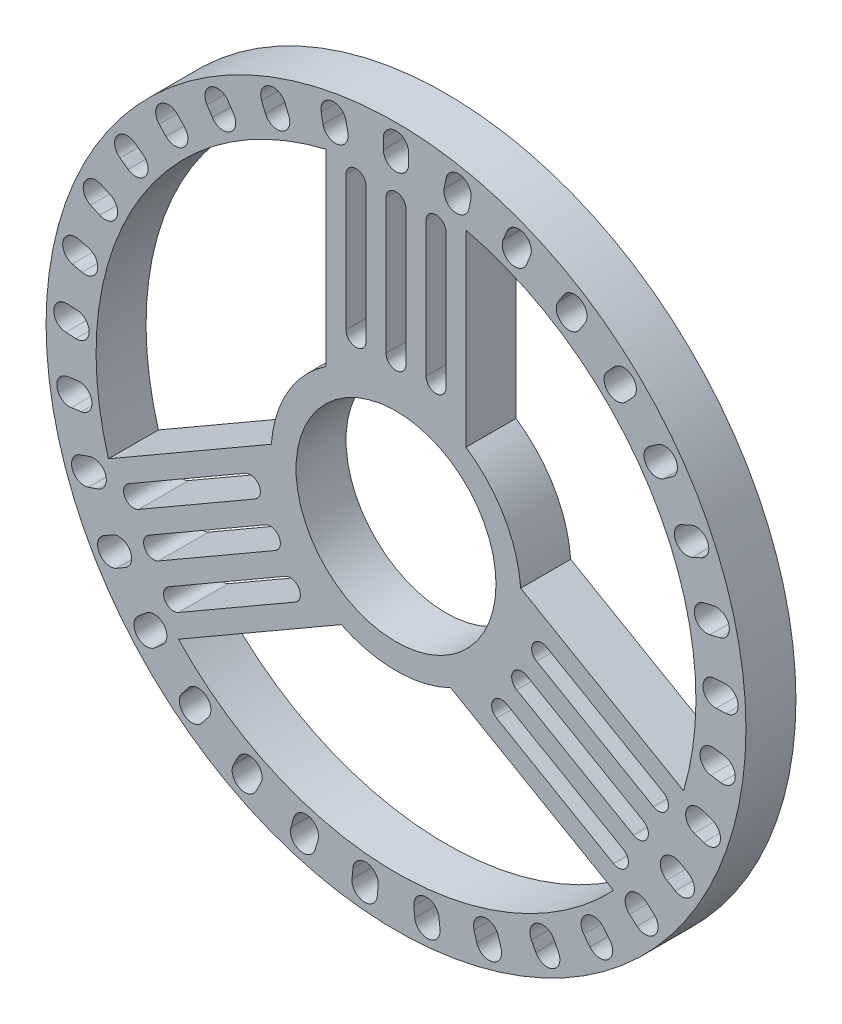
SolidWorks part; units mm, degrees
ref_plane "前视基准面" through (0, 0, 0) normal (0, 0, 1) x (1, 0, 0)
ref_plane "上视基准面" through (0, 0, 0) normal (0, 1, 0) x (1, 0, 0)
ref_plane "右视基准面" through (0, 0, 0) normal (1, 0, 0) x (0, 0, -1)
sketch "草图1" plane through (0, 0, 0) normal (0, 0, 1) x (1, 0, 0)
  line L0 (2.7274, -5.6161) -> (10.8818, -10.3241)
  line L1 (6.2305, 0.4443) -> (14.3818, -4.2619)
  line L2 (0, 16.5) -> (0, 16) construction
  line L3 (0.6338, 16.5) -> (0.6338, 16)
  line L4 (-0.6338, 16.5) -> (-0.6338, 16)
  line L5 (3.1226, 16.2018) -> (3.028, 15.7109) construction
  line L6 (3.745, 16.0819) -> (3.6504, 15.5909)
  line L7 (2.5003, 16.3218) -> (2.4057, 15.8308)
  line L8 (6.1324, 15.3181) -> (5.9466, 14.8539) construction
  line L9 (6.7208, 15.0825) -> (6.535, 14.6183)
  line L10 (5.544, 15.5536) -> (5.3582, 15.0894)
  line L11 (8.9206, 13.8807) -> (8.6503, 13.4601) construction
  line L12 (9.4538, 13.538) -> (9.1834, 13.1174)
  line L13 (8.3874, 14.2233) -> (8.1171, 13.8027)
  line L14 (11.3863, 11.9416) -> (11.0413, 11.5797) construction
  line L15 (11.845, 11.5042) -> (11.5, 11.1424)
  line L16 (10.9276, 12.379) -> (10.5826, 12.0171)
  line L17 (13.4405, 9.5709) -> (13.0332, 9.2809) construction
  line L18 (13.8081, 9.0547) -> (13.4009, 8.7646)
  line L19 (13.0729, 10.0872) -> (12.6656, 9.7972)
  line L20 (15.0089, 6.8543) -> (14.5541, 6.6466) construction
  line L21 (15.2722, 6.2778) -> (14.8174, 6.0701)
  line L22 (14.7456, 7.4309) -> (14.2908, 7.2232)
  line L23 (16.0349, 3.89) -> (15.549, 3.7721) construction
  line L24 (16.1843, 3.2741) -> (15.6984, 3.1562)
  line L25 (15.8855, 4.506) -> (15.3996, 4.3881)
  line L26 (16.4813, 0.7851) -> (15.9819, 0.7613) construction
  line L27 (16.5115, 0.152) -> (16.012, 0.1282)
  line L28 (16.4512, 1.4182) -> (15.9517, 1.3944)
  line L29 (16.3321, -2.3482) -> (15.8371, -2.277) construction
  line L30 (16.2419, -2.9755) -> (15.7469, -2.9044)
  line L31 (16.4223, -1.7208) -> (15.9273, -1.6497)
  line L32 (15.5925, -5.3966) -> (15.12, -5.2331) construction
  line L33 (15.3852, -5.9956) -> (14.9127, -5.832)
  line L34 (15.7998, -4.7977) -> (15.3273, -4.6341)
  line L35 (14.2894, -8.25) -> (13.8564, -8) construction
  line L36 (13.9725, -8.7989) -> (13.5395, -8.5489)
  line L37 (14.6063, -7.7011) -> (14.1733, -7.4511)
  line L38 (12.4699, -10.8052) -> (12.092, -10.4778) construction
  line L39 (12.0548, -11.2842) -> (11.6769, -10.9568)
  line L40 (12.8849, -10.3262) -> (12.507, -9.9988)
  line L41 (10.1996, -12.9699) -> (9.8905, -12.5768) construction
  line L42 (9.7014, -13.3617) -> (9.3923, -12.9686)
  line L43 (10.6978, -12.5781) -> (10.3887, -12.1851)
  line L44 (7.5607, -14.6658) -> (7.3316, -14.2214) construction
  line L45 (6.9974, -14.9562) -> (6.7683, -14.5118)
  line L46 (8.1241, -14.3754) -> (7.895, -13.9309)
  line L47 (4.6486, -15.8316) -> (4.5077, -15.3519) construction
  line L48 (4.0405, -16.0102) -> (3.8996, -15.5305)
  line L49 (5.2567, -15.6531) -> (5.1159, -15.1733)
  line L50 (1.5684, -16.4253) -> (1.5209, -15.9276) construction
  line L51 (0.9375, -16.4855) -> (0.89, -15.9878)
  line L52 (2.1994, -16.365) -> (2.1518, -15.8673)
  line L53 (-1.5684, -16.4253) -> (-1.5209, -15.9276) construction
  line L54 (-2.1994, -16.365) -> (-2.1518, -15.8673)
  line L55 (-0.9375, -16.4855) -> (-0.89, -15.9878)
  line L56 (-4.6486, -15.8316) -> (-4.5077, -15.3519) construction
  line L57 (-5.2567, -15.6531) -> (-5.1159, -15.1733)
  line L58 (-4.0405, -16.0102) -> (-3.8996, -15.5305)
  line L59 (-7.5607, -14.6658) -> (-7.3316, -14.2214) construction
  line L60 (-8.1241, -14.3754) -> (-7.895, -13.9309)
  line L61 (-6.9974, -14.9562) -> (-6.7683, -14.5118)
  line L62 (-10.1996, -12.9699) -> (-9.8905, -12.5768) construction
  line L63 (-10.6978, -12.5781) -> (-10.3887, -12.1851)
  line L64 (-9.7014, -13.3617) -> (-9.3923, -12.9686)
  line L65 (-12.4699, -10.8052) -> (-12.092, -10.4778) construction
  line L66 (-12.8849, -10.3262) -> (-12.507, -9.9988)
  line L67 (-12.0548, -11.2842) -> (-11.6769, -10.9568)
  line L68 (-14.2894, -8.25) -> (-13.8564, -8) construction
  line L69 (-14.6063, -7.7011) -> (-14.1733, -7.4511)
  line L70 (-13.9725, -8.7989) -> (-13.5395, -8.5489)
  line L71 (-15.5925, -5.3966) -> (-15.12, -5.2331) construction
  line L72 (-15.7998, -4.7977) -> (-15.3273, -4.6341)
  line L73 (-15.3852, -5.9956) -> (-14.9127, -5.832)
  line L74 (-16.3321, -2.3482) -> (-15.8371, -2.277) construction
  line L75 (-16.4223, -1.7208) -> (-15.9273, -1.6497)
  line L76 (-16.2419, -2.9755) -> (-15.7469, -2.9044)
  line L77 (-16.4813, 0.7851) -> (-15.9819, 0.7613) construction
  line L78 (-16.4512, 1.4182) -> (-15.9517, 1.3944)
  line L79 (-16.5115, 0.152) -> (-16.012, 0.1282)
  line L80 (-16.0349, 3.89) -> (-15.549, 3.7721) construction
  line L81 (-15.8855, 4.506) -> (-15.3996, 4.3881)
  line L82 (-16.1843, 3.2741) -> (-15.6984, 3.1562)
  line L83 (-15.0089, 6.8543) -> (-14.5541, 6.6466) construction
  line L84 (-14.7456, 7.4309) -> (-14.2908, 7.2232)
  line L85 (-15.2722, 6.2778) -> (-14.8174, 6.0701)
  line L86 (-13.4405, 9.5709) -> (-13.0332, 9.2809) construction
  line L87 (-13.0729, 10.0872) -> (-12.6656, 9.7972)
  line L88 (-13.8081, 9.0547) -> (-13.4009, 8.7646)
  line L89 (-11.3863, 11.9416) -> (-11.0413, 11.5797) construction
  line L90 (-10.9276, 12.379) -> (-10.5826, 12.0171)
  line L91 (-11.845, 11.5042) -> (-11.5, 11.1424)
  line L92 (-8.9206, 13.8807) -> (-8.6503, 13.4601) construction
  line L93 (-8.3874, 14.2233) -> (-8.1171, 13.8027)
  line L94 (-9.4538, 13.538) -> (-9.1834, 13.1174)
  line L95 (-6.1324, 15.3181) -> (-5.9466, 14.8539) construction
  line L96 (-5.544, 15.5536) -> (-5.3582, 15.0894)
  line L97 (-6.7208, 15.0825) -> (-6.535, 14.6183)
  line L98 (-3.1226, 16.2018) -> (-3.028, 15.7109) construction
  line L99 (-2.5003, 16.3218) -> (-2.4057, 15.8308)
  line L100 (-3.745, 16.0819) -> (-3.6504, 15.5909)
  line L101 (12.1234, -6.9994) -> (6.283, -3.6275) construction
  line L102 (3.5, 5.1701) -> (3.5, 14.586)
  line L103 (-3.5, 5.1736) -> (-3.5, 14.586)
  line L104 (11.8737, -7.4319) -> (6.0333, -4.0599)
  line L105 (12.3731, -6.567) -> (6.5326, -3.195)
  line L106 (11.1234, -8.7315) -> (5.283, -5.3595) construction
  line L107 (0, 13.9989) -> (0, 7.2549) construction
  line L108 (0.4994, 13.9989) -> (0.4994, 7.2549)
  line L109 (-0.4994, 13.9989) -> (-0.4994, 7.2549)
  line L110 (2, 13.9989) -> (2, 7.2549) construction
  line L111 (2.4994, 13.9989) -> (2.4994, 7.2549)
  line L112 (1.5006, 13.9989) -> (1.5006, 7.2549)
  line L113 (-2, 13.9989) -> (-2, 7.2549) construction
  line L114 (-1.5006, 13.9989) -> (-1.5006, 7.2549)
  line L115 (-2.4994, 13.9989) -> (-2.4994, 7.2549)
  line L116 (10.8737, -9.164) -> (5.0333, -5.792)
  line L117 (11.3731, -8.299) -> (5.5326, -4.9271)
  line L118 (13.1234, -5.2674) -> (7.283, -1.8954) construction
  line L119 (12.8737, -5.6998) -> (7.0333, -2.3279)
  line L120 (13.3731, -4.8349) -> (7.5326, -1.463)
  line L121 (-6.2274, 0.4461) -> (-14.3818, -4.2619)
  line L122 (-2.7305, -5.6179) -> (-10.8818, -10.3241)
  line L123 (-12.1234, -6.9994) -> (-6.283, -3.6275) construction
  line L124 (-12.3731, -6.567) -> (-6.5326, -3.195)
  line L125 (-11.8737, -7.4319) -> (-6.0333, -4.0599)
  line L126 (-13.1234, -5.2674) -> (-7.283, -1.8954) construction
  line L127 (-13.3731, -4.8349) -> (-7.5326, -1.463)
  line L128 (-12.8737, -5.6998) -> (-7.0333, -2.3279)
  line L129 (-11.1234, -8.7315) -> (-5.283, -5.3595) construction
  line L130 (-11.3731, -8.299) -> (-5.5326, -4.9271)
  line L131 (-10.8737, -9.164) -> (-5.0333, -5.792)
  circle A0 centre (0, 0) radius 17.5
  circle A1 centre (0, 0) radius 15
  circle A2 centre (0, 0) radius 5
  circle A3 centre (0, 0) radius 6.25
  arc A4 (0.6338, 16.5) -> (-0.6338, 16.5) centre (0, 16.5) ccw
  arc A5 (-0.6338, 16) -> (0.6338, 16) centre (0, 16) ccw
  arc A6 (3.745, 16.0819) -> (2.5003, 16.3218) centre (3.1226, 16.2018) ccw
  arc A7 (2.4057, 15.8308) -> (3.6504, 15.5909) centre (3.028, 15.7109) ccw
  arc A8 (6.7208, 15.0825) -> (5.544, 15.5536) centre (6.1324, 15.3181) ccw
  arc A9 (5.3582, 15.0894) -> (6.535, 14.6183) centre (5.9466, 14.8539) ccw
  arc A10 (9.4538, 13.538) -> (8.3874, 14.2233) centre (8.9206, 13.8807) ccw
  arc A11 (8.1171, 13.8027) -> (9.1834, 13.1174) centre (8.6503, 13.4601) ccw
  arc A12 (11.845, 11.5042) -> (10.9276, 12.379) centre (11.3863, 11.9416) ccw
  arc A13 (10.5826, 12.0171) -> (11.5, 11.1424) centre (11.0413, 11.5797) ccw
  arc A14 (13.8081, 9.0547) -> (13.0729, 10.0872) centre (13.4405, 9.5709) ccw
  arc A15 (12.6656, 9.7972) -> (13.4009, 8.7646) centre (13.0332, 9.2809) ccw
  arc A16 (15.2722, 6.2778) -> (14.7456, 7.4309) centre (15.0089, 6.8543) ccw
  arc A17 (14.2908, 7.2232) -> (14.8174, 6.0701) centre (14.5541, 6.6466) ccw
  arc A18 (16.1843, 3.2741) -> (15.8855, 4.506) centre (16.0349, 3.89) ccw
  arc A19 (15.3996, 4.3881) -> (15.6984, 3.1562) centre (15.549, 3.7721) ccw
  arc A20 (16.5115, 0.152) -> (16.4512, 1.4182) centre (16.4813, 0.7851) ccw
  arc A21 (15.9517, 1.3944) -> (16.012, 0.1282) centre (15.9819, 0.7613) ccw
  arc A22 (16.2419, -2.9755) -> (16.4223, -1.7208) centre (16.3321, -2.3482) ccw
  arc A23 (15.9273, -1.6497) -> (15.7469, -2.9044) centre (15.8371, -2.277) ccw
  arc A24 (15.3852, -5.9956) -> (15.7998, -4.7977) centre (15.5925, -5.3966) ccw
  arc A25 (15.3273, -4.6341) -> (14.9127, -5.832) centre (15.12, -5.2331) ccw
  arc A26 (13.9725, -8.7989) -> (14.6063, -7.7011) centre (14.2894, -8.25) ccw
  arc A27 (14.1733, -7.4511) -> (13.5395, -8.5489) centre (13.8564, -8) ccw
  arc A28 (12.0548, -11.2842) -> (12.8849, -10.3262) centre (12.4699, -10.8052) ccw
  arc A29 (12.507, -9.9988) -> (11.6769, -10.9568) centre (12.092, -10.4778) ccw
  arc A30 (9.7014, -13.3617) -> (10.6978, -12.5781) centre (10.1996, -12.9699) ccw
  arc A31 (10.3887, -12.1851) -> (9.3923, -12.9686) centre (9.8905, -12.5768) ccw
  arc A32 (6.9974, -14.9562) -> (8.1241, -14.3754) centre (7.5607, -14.6658) ccw
  arc A33 (7.895, -13.9309) -> (6.7683, -14.5118) centre (7.3316, -14.2214) ccw
  arc A34 (4.0405, -16.0102) -> (5.2567, -15.6531) centre (4.6486, -15.8316) ccw
  arc A35 (5.1159, -15.1733) -> (3.8996, -15.5305) centre (4.5077, -15.3519) ccw
  arc A36 (0.9375, -16.4855) -> (2.1994, -16.365) centre (1.5684, -16.4253) ccw
  arc A37 (2.1518, -15.8673) -> (0.89, -15.9878) centre (1.5209, -15.9276) ccw
  arc A38 (-2.1994, -16.365) -> (-0.9375, -16.4855) centre (-1.5684, -16.4253) ccw
  arc A39 (-0.89, -15.9878) -> (-2.1518, -15.8673) centre (-1.5209, -15.9276) ccw
  arc A40 (-5.2567, -15.6531) -> (-4.0405, -16.0102) centre (-4.6486, -15.8316) ccw
  arc A41 (-3.8996, -15.5305) -> (-5.1159, -15.1733) centre (-4.5077, -15.3519) ccw
  arc A42 (-8.1241, -14.3754) -> (-6.9974, -14.9562) centre (-7.5607, -14.6658) ccw
  arc A43 (-6.7683, -14.5118) -> (-7.895, -13.9309) centre (-7.3316, -14.2214) ccw
  arc A44 (-10.6978, -12.5781) -> (-9.7014, -13.3617) centre (-10.1996, -12.9699) ccw
  arc A45 (-9.3923, -12.9686) -> (-10.3887, -12.1851) centre (-9.8905, -12.5768) ccw
  arc A46 (-12.8849, -10.3262) -> (-12.0548, -11.2842) centre (-12.4699, -10.8052) ccw
  arc A47 (-11.6769, -10.9568) -> (-12.507, -9.9988) centre (-12.092, -10.4778) ccw
  arc A48 (-14.6063, -7.7011) -> (-13.9725, -8.7989) centre (-14.2894, -8.25) ccw
  arc A49 (-13.5395, -8.5489) -> (-14.1733, -7.4511) centre (-13.8564, -8) ccw
  arc A50 (-15.7998, -4.7977) -> (-15.3852, -5.9956) centre (-15.5925, -5.3966) ccw
  arc A51 (-14.9127, -5.832) -> (-15.3273, -4.6341) centre (-15.12, -5.2331) ccw
  arc A52 (-16.4223, -1.7208) -> (-16.2419, -2.9755) centre (-16.3321, -2.3482) ccw
  arc A53 (-15.7469, -2.9044) -> (-15.9273, -1.6497) centre (-15.8371, -2.277) ccw
  arc A54 (-16.4512, 1.4182) -> (-16.5115, 0.152) centre (-16.4813, 0.7851) ccw
  arc A55 (-16.012, 0.1282) -> (-15.9517, 1.3944) centre (-15.9819, 0.7613) ccw
  arc A56 (-15.8855, 4.506) -> (-16.1843, 3.2741) centre (-16.0349, 3.89) ccw
  arc A57 (-15.6984, 3.1562) -> (-15.3996, 4.3881) centre (-15.549, 3.7721) ccw
  arc A58 (-14.7456, 7.4309) -> (-15.2722, 6.2778) centre (-15.0089, 6.8543) ccw
  arc A59 (-14.8174, 6.0701) -> (-14.2908, 7.2232) centre (-14.5541, 6.6466) ccw
  arc A60 (-13.0729, 10.0872) -> (-13.8081, 9.0547) centre (-13.4405, 9.5709) ccw
  arc A61 (-13.4009, 8.7646) -> (-12.6656, 9.7972) centre (-13.0332, 9.2809) ccw
  arc A62 (-10.9276, 12.379) -> (-11.845, 11.5042) centre (-11.3863, 11.9416) ccw
  arc A63 (-11.5, 11.1424) -> (-10.5826, 12.0171) centre (-11.0413, 11.5797) ccw
  arc A64 (-8.3874, 14.2233) -> (-9.4538, 13.538) centre (-8.9206, 13.8807) ccw
  arc A65 (-9.1834, 13.1174) -> (-8.1171, 13.8027) centre (-8.6503, 13.4601) ccw
  arc A66 (-5.544, 15.5536) -> (-6.7208, 15.0825) centre (-6.1324, 15.3181) ccw
  arc A67 (-6.535, 14.6183) -> (-5.3582, 15.0894) centre (-5.9466, 14.8539) ccw
  arc A68 (-2.5003, 16.3218) -> (-3.745, 16.0819) centre (-3.1226, 16.2018) ccw
  arc A69 (-3.6504, 15.5909) -> (-2.4057, 15.8308) centre (-3.028, 15.7109) ccw
  arc A70 (0.4994, 13.9989) -> (-0.4994, 13.9989) centre (0, 13.9989) ccw
  arc A71 (-0.4994, 7.2549) -> (0.4994, 7.2549) centre (0, 7.2549) ccw
  arc A72 (2.4994, 13.9989) -> (1.5006, 13.9989) centre (2, 13.9989) ccw
  arc A73 (1.5006, 7.2549) -> (2.4994, 7.2549) centre (2, 7.2549) ccw
  arc A74 (-1.5006, 13.9989) -> (-2.4994, 13.9989) centre (-2, 13.9989) ccw
  arc A75 (-2.4994, 7.2549) -> (-1.5006, 7.2549) centre (-2, 7.2549) ccw
  arc A76 (11.8737, -7.4319) -> (12.3731, -6.567) centre (12.1234, -6.9994) ccw
  arc A77 (6.5326, -3.195) -> (6.0333, -4.0599) centre (6.283, -3.6275) ccw
  arc A78 (10.8737, -9.164) -> (11.3731, -8.299) centre (11.1234, -8.7315) ccw
  arc A79 (5.5326, -4.9271) -> (5.0333, -5.792) centre (5.283, -5.3595) ccw
  arc A80 (12.8737, -5.6998) -> (13.3731, -4.8349) centre (13.1234, -5.2674) ccw
  arc A81 (7.5326, -1.463) -> (7.0333, -2.3279) centre (7.283, -1.8954) ccw
  arc A82 (-12.3731, -6.567) -> (-11.8737, -7.4319) centre (-12.1234, -6.9994) ccw
  arc A83 (-6.0333, -4.0599) -> (-6.5326, -3.195) centre (-6.283, -3.6275) ccw
  arc A84 (-13.3731, -4.8349) -> (-12.8737, -5.6998) centre (-13.1234, -5.2674) ccw
  arc A85 (-7.0333, -2.3279) -> (-7.5326, -1.463) centre (-7.283, -1.8954) ccw
  arc A86 (-11.3731, -8.299) -> (-10.8737, -9.164) centre (-11.1234, -8.7315) ccw
  arc A87 (-5.0333, -5.792) -> (-5.5326, -4.9271) centre (-5.283, -5.3595) ccw
  point P10 (0, 16.25)
  point P20 (3.0753, 15.9563)
  point P27 (6.0395, 15.086)
  point P34 (8.7854, 13.6704)
  point P41 (11.2138, 11.7607)
  point P48 (13.2369, 9.4259)
  point P55 (14.7815, 6.7505)
  point P62 (15.7919, 3.8311)
  point P69 (16.2316, 0.7732)
  point P76 (16.0846, -2.3126)
  point P83 (15.3563, -5.3149)
  point P90 (14.0729, -8.125)
  point P97 (12.2809, -10.6415)
  point P104 (10.0451, -12.7734)
  point P111 (7.4462, -14.4436)
  point P118 (4.5782, -15.5918)
  point P125 (1.5447, -16.1764)
  point P132 (-1.5447, -16.1764)
  point P139 (-4.5782, -15.5918)
  point P146 (-7.4462, -14.4436)
  point P153 (-10.0451, -12.7734)
  point P160 (-12.2809, -10.6415)
  point P167 (-14.0729, -8.125)
  point P174 (-15.3563, -5.3149)
  point P181 (-16.0846, -2.3126)
  point P188 (-16.2316, 0.7732)
  point P195 (-15.7919, 3.8311)
  point P202 (-14.7815, 6.7505)
  point P209 (-13.2369, 9.4259)
  point P216 (-11.2138, 11.7607)
  point P223 (-8.7854, 13.6704)
  point P230 (-6.0395, 15.086)
  point P237 (-3.0753, 15.9563)
  point P242 (0, 0)
  point P249 (9.2032, -5.3135)
  point P251 (0, 10.6269)
  point P260 (2, 10.6269)
  point P267 (-2, 10.6269)
  point P277 (8.2032, -7.0455)
  point P284 (10.2032, -3.5814)
  point P295 (-9.2032, -5.3135)
  point P302 (-10.2032, -3.5814)
  point P309 (-8.2032, -7.0455)
  point P315 (0, 0)
  dimension "D1" = 35
  dimension "D2" = 30
  dimension "D3" = 10
  dimension "D4" = 12.5
  dimension "D5" = 3
  dimension "D7" = 33
extrude "凸台-拉伸2" add sketch "草图1" along normal blind 2.5
sketch "草图2" plane through (0, 0, 0) normal (0, 0, 1) x (1, 0, 0)
  line L46 (3.5, 5.1781) -> (3.5, 14.586) construction
  line L47 (-3.5, 5.1781) -> (-3.5, 14.586) construction
  line L48 (3.6504, 15.5909) -> (3.745, 16.0819)
  line L49 (2.5003, 16.3218) -> (2.4057, 15.8308)
  line L50 (3.6504, 15.5909) -> (3.745, 16.0819)
  line L51 (2.5003, 16.3218) -> (2.4057, 15.8308)
  line L52 (-3.745, 16.0819) -> (-3.6504, 15.5909) construction
  line L53 (-2.5003, 16.3218) -> (-2.4057, 15.8308) construction
  line L54 (0.6338, 16.5) -> (0.6338, 16) construction
  line L55 (-0.6338, 16.5) -> (-0.6338, 16) construction
  line L56 (-2.4994, 13.9989) -> (-2.4994, 7.2549) construction
  line L57 (-1.5006, 13.9989) -> (-1.5006, 7.2549) construction
  line L58 (1.5006, 13.9989) -> (1.5006, 7.2549) construction
  line L59 (2.4994, 13.9989) -> (2.4994, 7.2549) construction
  line L60 (-0.4994, 13.9989) -> (-0.4994, 7.2549) construction
  line L61 (0.4994, 13.9989) -> (0.4994, 7.2549) construction
  line L62 (3.5, 5.1781) -> (3.5, 14.586)
  line L63 (-3.5, 5.1781) -> (-3.5, 14.586)
  line L64 (-3.745, 16.0819) -> (-3.6504, 15.5909)
  line L65 (-2.5003, 16.3218) -> (-2.4057, 15.8308)
  line L66 (0.6338, 16.5) -> (0.6338, 16)
  line L67 (-0.6338, 16.5) -> (-0.6338, 16)
  line L68 (-2.4994, 13.9989) -> (-2.4994, 7.2549)
  line L69 (-1.5006, 13.9989) -> (-1.5006, 7.2549)
  line L70 (1.5006, 13.9989) -> (1.5006, 7.2549)
  line L71 (2.4994, 13.9989) -> (2.4994, 7.2549)
  line L72 (-0.4994, 13.9989) -> (-0.4994, 7.2549)
  line L73 (0.4994, 13.9989) -> (0.4994, 7.2549)
  circle A37 centre (0, 0) radius 17.5
  circle A38 centre (0, 0) radius 17.5
  arc A65 (-3.5, 14.586) -> (-14.3818, -4.2619) centre (0, 0) ccw construction
  arc A66 (-3.5, 14.586) -> (-14.3818, -4.2619) centre (0, 0) ccw
  arc A67 (2.4057, 15.8308) -> (3.6504, 15.5909) centre (3.028, 15.7109) ccw
  arc A68 (3.745, 16.0819) -> (2.5003, 16.3218) centre (3.1226, 16.2018) ccw
  arc A69 (2.4057, 15.8308) -> (3.6504, 15.5909) centre (3.028, 15.7109) ccw
  arc A70 (3.745, 16.0819) -> (2.5003, 16.3218) centre (3.1226, 16.2018) ccw
  arc A71 (-0.6338, 16) -> (0.6338, 16) centre (0, 16) ccw construction
  arc A72 (-0.6338, 16) -> (0.6338, 16) centre (0, 16) ccw
  arc A73 (0.6338, 16.5) -> (-0.6338, 16.5) centre (0, 16.5) ccw construction
  arc A74 (1.5006, 7.2549) -> (2.4994, 7.2549) centre (2, 7.2549) ccw construction
  arc A75 (14.3818, -4.2619) -> (3.5, 14.586) centre (0, 0) ccw construction
  arc A76 (-3.6504, 15.5909) -> (-2.4057, 15.8308) centre (-3.028, 15.7109) ccw construction
  arc A77 (-2.5003, 16.3218) -> (-3.745, 16.0819) centre (-3.1226, 16.2018) ccw construction
  arc A78 (-2.4994, 7.2549) -> (-1.5006, 7.2549) centre (-2, 7.2549) ccw construction
  arc A79 (-1.5006, 13.9989) -> (-2.4994, 13.9989) centre (-2, 13.9989) ccw construction
  arc A80 (2.4994, 13.9989) -> (1.5006, 13.9989) centre (2, 13.9989) ccw construction
  arc A81 (-0.4994, 7.2549) -> (0.4994, 7.2549) centre (0, 7.2549) ccw construction
  arc A82 (0.4994, 13.9989) -> (-0.4994, 13.9989) centre (0, 13.9989) ccw construction
  arc A83 (1.5006, 7.2549) -> (2.4994, 7.2549) centre (2, 7.2549) ccw
  arc A84 (14.3818, -4.2619) -> (3.5, 14.586) centre (0, 0) ccw
  arc A85 (-3.6504, 15.5909) -> (-2.4057, 15.8308) centre (-3.028, 15.7109) ccw
  arc A86 (-2.5003, 16.3218) -> (-3.745, 16.0819) centre (-3.1226, 16.2018) ccw
  arc A87 (0.6338, 16.5) -> (-0.6338, 16.5) centre (0, 16.5) ccw
  arc A88 (-2.4994, 7.2549) -> (-1.5006, 7.2549) centre (-2, 7.2549) ccw
  arc A89 (-1.5006, 13.9989) -> (-2.4994, 13.9989) centre (-2, 13.9989) ccw
  arc A90 (2.4994, 13.9989) -> (1.5006, 13.9989) centre (2, 13.9989) ccw
  arc A91 (-0.4994, 7.2549) -> (0.4994, 7.2549) centre (0, 7.2549) ccw
  arc A92 (0.4994, 13.9989) -> (-0.4994, 13.9989) centre (0, 13.9989) ccw
  arc A93 (-3.5, 5.1781) -> (-6.2343, 0.442) centre (0, 0) ccw construction
  arc A94 (6.2343, 0.442) -> (3.5, 5.1781) centre (0, 0) ccw construction
  circle A95 centre (0, 0) radius 5 construction
  arc A96 (-3.5, 5.1781) -> (-6.2343, 0.442) centre (0, 0) ccw
  arc A97 (6.2343, 0.442) -> (3.5, 5.1781) centre (0, 0) ccw
  circle A98 centre (0, 0) radius 5
  arc A99 (-10.9276, 12.379) -> (-11.845, 11.5042) centre (-11.3863, 11.9416) ccw construction
  arc A100 (-10.9276, 12.379) -> (-11.845, 11.5042) centre (-11.3863, 11.9416) ccw
  point P18 (0, 0)
  dimension "D2" = 0
  dimension "D1" = 0
